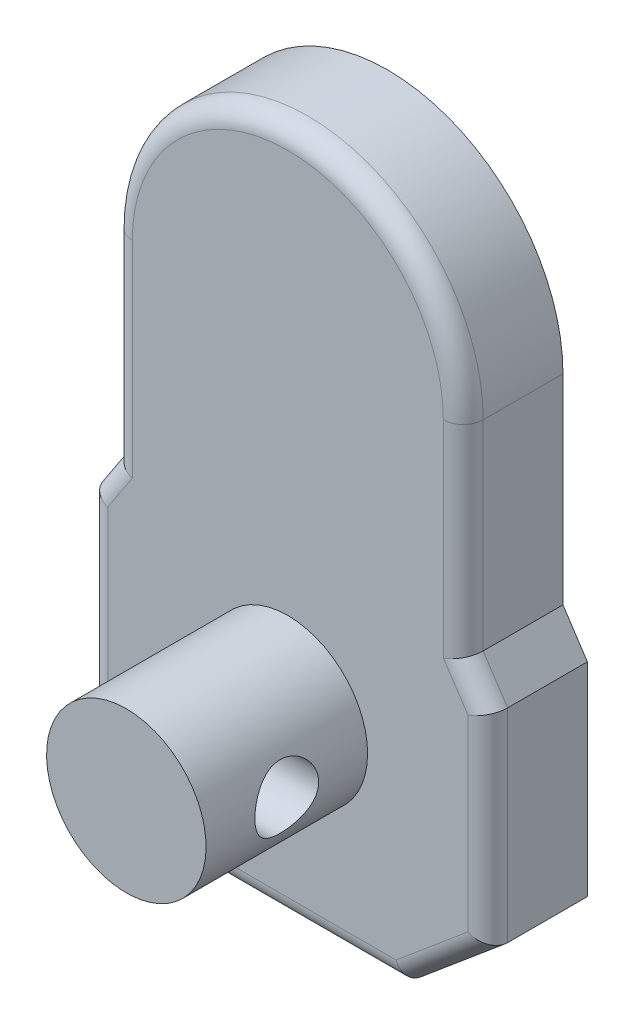
SolidWorks part; units mm, degrees
material "PW100:Mi:0:1:Ar:0:-1:C1:1:2:3:Re:27:"
ref_plane "Front" through (0, 0, 0) normal (0, 0, 1) x (1, 0, 0)
ref_plane "Top" through (0, 0, 0) normal (0, 1, 0) x (1, 0, 0)
ref_plane "Right" through (0, 0, 0) normal (1, 0, 0) x (0, 0, -1)
sketch "Support-Front-Cylinder" plane through (0, 0, 0) normal (0, 0, 1) x (1, 0, 0)
  line L0 (0, -23) -> (0, 50.4) construction
  line L1 (20.05, 0) -> (-20.05, 0) construction
  line L23 (-9.0631, 28.5738) -> (9.0631, 37.0262) construction
  line L28 (5.4164, -18.5) -> (5.4164, -20)
  line L32 (16, -9) -> (-16, 9) construction
  line L33 (-16, -9) -> (16, 9) construction
  line L34 (5.4164, -20) -> (-5.4164, -20)
  line L35 (-5.4164, -18.5) -> (-5.4164, -20)
  line L45 (0, -18.5) -> (-5.4164, -17.0487) construction
  line L46 (-20.05, 9) -> (-17.6, 12.7206)
  line L47 (20.05, 0) -> (20.05, -11.4)
  line L48 (-5.373, 24.3661) -> (0, 32.8) construction
  line L49 (-20.05, 0) -> (-20.05, -11.4)
  line L50 (-9.0631, 28.5738) -> (-5.373, 24.3661) construction
  line L51 (20.05, -11.4) -> (11.5885, -18.5)
  line L52 (-13.75, 0) -> (-7.0166, -18.5)
  line L53 (-7.0166, -18.5) -> (7.0166, -18.5)
  line L54 (0, -18.5) -> (0, -23) construction
  line L55 (13.75, 0) -> (7.0166, -18.5)
  line L56 (-20.05, -11.4) -> (-11.5885, -18.5)
  line L57 (11.5885, -18.5) -> (7.0166, -18.5)
  line L58 (-11.5885, -18.5) -> (-7.0166, -18.5)
  line L59 (20.05, -11.4) -> (-20.05, -11.4) construction
  line L60 (20.05, 0) -> (20.05, 9)
  line L61 (-20.05, 0) -> (-20.05, 9)
  line L62 (17.6, 12.7206) -> (17.6, 32.8)
  line L63 (-17.6, 12.7206) -> (-17.6, 32.8)
  line L64 (2.5, -20) -> (2.5, -23)
  line L65 (-2.5, -20) -> (-2.5, -23)
  line L66 (2.5, -23) -> (-2.5, -23)
  line L67 (-11.7451, 0.3392) -> (-5.4164, -17.0487)
  line L68 (11.7451, 0.3392) -> (5.4164, -17.0487)
  line L69 (5.4164, -17.0487) -> (-5.4164, -17.0487)
  line L70 (5.4164, -18.5) -> (5.4164, -17.0487) construction
  line L71 (-5.4164, -18.5) -> (-5.4164, -17.0487) construction
  line L72 (17.6, 32.8) -> (-17.6, 32.8) construction
  line L73 (20.05, 9) -> (17.6, 12.7206)
  line L75 (-5.373, 24.3661) -> (0, 22.8) construction
  circle A18 centre (0, 0) radius 9.65
  circle A29 centre (16, 9) radius 2.4
  arc A30 (13.75, 0) -> (-13.75, 0) centre (0, 0) ccw
  circle A31 centre (-16, 9) radius 2.4
  circle A32 centre (-16, -9) radius 2.4
  circle A33 centre (16, -9) radius 2.4
  arc A34 (20.05, 9) -> (17.6, 12.7206) centre (16, 9) ccw
  arc A35 (-20.05, 9) -> (-17.6, 12.7206) centre (-16, 9) cw
  arc A36 (17.6, 32.8) -> (0, 50.4) centre (0, 32.8) ccw
  arc A37 (-17.6, 32.8) -> (0, 50.4) centre (0, 32.8) cw
  arc A38 (17.6, 32.8) -> (-17.6, 32.8) centre (0, 32.8) cw
  arc A39 (11.7451, 0.3392) -> (-11.7451, 0.3392) centre (0, 0) ccw
  arc A40 (13.75, 0) -> (-13.75, 0) centre (0, 0) cw construction
  circle A41 centre (0, 32.8) radius 10
  circle A42 centre (-5.373, 24.3661) radius 2.5
  circle A43 centre (-9.0631, 28.5738) radius 3.75
  circle A44 centre (9.0631, 37.0262) radius 2.5
  circle A45 centre (-5.373, 24.3661) radius 0.75
  circle A46 centre (9.0631, 37.0262) radius 0.75
  point P3 (0, 0)
  point P6 (0, 0)
  point P16 (0, -20)
  dimension "D4" = 4.8
  dimension "D5" = 1.5
  dimension "D14" = 3
  dimension "D15" = 73.4
  dimension "D20" = 1.5
  dimension "D21" = 25
  dimension "D10" = 19.3
  dimension "D24" = 27.5
  dimension "D12" = 35.2
  dimension "D17" = 20
  dimension "D18" = 5
  dimension "D19" = 7.5
  dimension "D3" = 40.1
  dimension "D6" = 18.5
  dimension "D7" = 32
  dimension "D8" = 18
  dimension "D9" = 100
  dimension "D16" = 2
  dimension "D22" = 15
  dimension "D23" = 32.8
  dimension "D26" = 40
  dimension "Thickn-Elect" = 5
sketch "Support-Right" plane through (0, 0, 0) normal (1, 0, 0) x (0, 0, -1)
  line L0 (96.6074, 0) -> (-156.5, 0) construction
  line L1 (-140.3, -18.5) -> (-140.3, 50.4)
  line L2 (0, -18.5) -> (0, 13.75)
  line L3 (0, 13.75) -> (-90.3, 13.75)
  line L4 (87.4074, 9.65) -> (96.6074, 9.65)
  line L5 (-140.3, 50.4) -> (-95.3, 50.4)
  line L6 (-90.3, 15.2) -> (-85.3, 15.2)
  line L7 (-95.3, 50.4) -> (-95.3, -18.5)
  line L8 (-85.3, 15.2) -> (-85.3, 50.4) construction
  line L9 (-11.7, 17.7) -> (-11.7, 47.9)
  line L10 (-14.2, 50.4) -> (-90.3, 50.4)
  line L11 (-85.3, 50.4) -> (-84.9, 50.8)
  line L12 (-95.3, -18.5) -> (-140.3, -18.5)
  line L13 (-95.3, 50.4) -> (-90.3, 50.4)
  line L14 (-90.3, 50.4) -> (-90.3, 15.2)
  line L15 (0, 9.65) -> (-31, 9.65) construction
  line L16 (-90.3, 15.2) -> (-90.3, -18.5)
  line L17 (-90.3, -18.5) -> (-95.3, -18.5)
  line L18 (-85.3, 15.2) -> (-85.3, -18.5) construction
  line L19 (-90.3, -18.5) -> (0, -18.5)
  line L20 (-140.3, -20.75) -> (-140.3, -18.5) construction
  line L21 (-140.3, 32.8) -> (-9.2, 32.8) construction
  line L22 (-9.2, 50.4) -> (-9.2, 15.2) construction
  line L23 (-9.2, 15.2) -> (-11.7, 15.2) construction
  line L24 (-9.2, 50.4) -> (-11.7, 50.4) construction
  line L25 (-156.5, 8) -> (-156.5, -8)
  line L26 (-156.5, -8) -> (-140.3, -8)
  line L27 (-84.9, 50.8) -> (-90.7, 50.8)
  line L28 (-90.7, 50.8) -> (-90.3, 50.4)
  line L29 (-156.5, 8) -> (-140.3, 8)
  line L30 (-14, 13.75) -> (-14, -18.5) construction
  line L31 (-90.7, 14.8) -> (-90.3, 15.2)
  line L32 (96.6074, 9.65) -> (96.6074, -9.65)
  line L35 (87.4074, 9.65) -> (-106.9074, 9.65)
  line L36 (-106.9074, 9.65) -> (-106.9074, -9.65)
  line L37 (87.4074, -9.65) -> (-106.9074, -9.65)
  line L38 (-84.9, 14.8) -> (-90.7, 14.8)
  line L40 (87.4074, -9.65) -> (96.6074, -9.65)
  line L41 (-17.5, 50.4) -> (0, 50.4) construction
  line L42 (-9.2, 32.8) -> (0, 32.8) construction
  line L43 (-85.3, 15.2) -> (-84.9, 14.8)
  line L44 (-121.6287, -20.75) -> (-120.4574, -18.5)
  line L45 (-130.7862, -20.75) -> (-131.9574, -18.5)
  line L46 (-121.6287, -20.75) -> (-130.7862, -20.75)
  line L47 (-106.9074, -9.65) -> (-126.2074, -9.65) construction
  line L48 (83.6574, 9.65) -> (82.4074, 8.4)
  line L49 (-126.2074, -9.65) -> (-126.2074, 9.65) construction
  line L50 (-31, 13.75) -> (-31, -18.5) construction
  line L51 (82.4074, 8.4) -> (81.1574, 9.65)
  line L52 (82.4074, 9.65) -> (82.4074, -9.65) construction
  line L53 (-85.3, 15.2) -> (0, 15.2)
  line L54 (-90.3, 50.4) -> (-17.5, 50.4) construction
  line L55 (82.4074, -8.4) -> (81.1574, -9.65)
  line L56 (83.6574, -9.65) -> (82.4074, -8.4)
  line L57 (-126.2074, 9.65) -> (-106.9074, 9.65) construction
  line L58 (0, 15.2) -> (0, 13.75) construction
  line L60 (0, -23) -> (0, -18.5) construction
  line L63 (-122.7862, -20.75) -> (-123.9574, -23)
  line L64 (0, -9.65) -> (-31, -9.65) construction
  line L69 (-123.9574, -23) -> (-128.4574, -23)
  line L70 (-126.2074, -23) -> (-126.2074, -18.5) construction
  line L71 (-140.3, -20.75) -> (0, -20.75) construction
  line L72 (-129.6287, -20.75) -> (-128.4574, -23)
  line L73 (-140.3, -20.75) -> (-140.3, -23) construction
  line L74 (-140.3, -23) -> (0, -23) construction
  line L75 (-130.3, 50.4) -> (-130.3, -18.5)
  arc A0 (-14.2, 50.4) -> (-11.7, 47.9) centre (-14.2, 47.9) cw
  arc A1 (-14.2, 15.2) -> (-11.7, 17.7) centre (-14.2, 17.7) ccw
  circle A2 centre (-148.4, 0) radius 3.2
  circle A3 centre (87.4074, 0) radius 3.2
  point P13 (-140.3, 32.8)
  point P18 (11.5, 0)
  point P44 (87.4074, 0)
  point P50 (-106.9074, 0)
  point P54 (96.6074, 0)
  point P61 (-11.7, 32.8)
  point P63 (-14, 0)
  point P71 (-196.35, 0)
ref_plane "Plane1" through (0, 0, 130.3) normal (0, 0, 1) x (1, 0, 0)
sketch "Sketch1" plane through (0, 0, 130.3) normal (0, 0, 1) x (1, 0, 0)
  line L0 (20.05, 9) -> (17.6, 12.7206) construction
  line L1 (-20.05, 9) -> (-17.6, 12.7206) construction
  line L2 (20.05, 9) -> (17.6, 12.7206)
  line L3 (-20.05, 0) -> (-20.05, 9) construction
  line L4 (-20.05, 0) -> (-20.05, -11.4) construction
  line L5 (-20.05, -11.4) -> (-11.5885, -18.5) construction
  line L6 (-11.5885, -18.5) -> (-7.0166, -18.5) construction
  line L7 (-17.6, 12.7206) -> (-17.6, 32.8) construction
  line L8 (-7.0166, -18.5) -> (7.0166, -18.5) construction
  line L9 (20.05, 0) -> (20.05, 9) construction
  line L10 (20.05, 0) -> (20.05, -11.4) construction
  line L11 (20.05, -11.4) -> (11.5885, -18.5) construction
  line L12 (11.5885, -18.5) -> (7.0166, -18.5) construction
  line L13 (17.6, 12.7206) -> (17.6, 32.8) construction
  line L14 (-20.05, 9) -> (-17.6, 12.7206)
  line L16 (-20.05, -11.4) -> (-11.5885, -18.5)
  line L18 (-17.6, 12.7206) -> (-17.6, 32.8)
  line L19 (-20.05, 0) -> (-20.05, 9)
  line L20 (-20.05, 0) -> (-20.05, -11.4)
  line L22 (-11.5885, -18.5) -> (-7.0166, -18.5)
  line L23 (-7.0166, -18.5) -> (7.0166, -18.5)
  line L24 (20.05, 0) -> (20.05, 9)
  line L25 (20.05, 0) -> (20.05, -11.4)
  line L26 (20.05, -11.4) -> (11.5885, -18.5)
  line L27 (11.5885, -18.5) -> (7.0166, -18.5)
  line L28 (17.6, 12.7206) -> (17.6, 32.8)
  arc A6 (0, 50.4) -> (-17.6, 32.8) centre (0, 32.8) ccw construction
  arc A7 (17.6, 32.8) -> (0, 50.4) centre (0, 32.8) ccw construction
  arc A14 (0, 50.4) -> (-17.6, 32.8) centre (0, 32.8) ccw
  arc A15 (17.6, 32.8) -> (0, 50.4) centre (0, 32.8) ccw
extrude "Body" add sketch "Sketch1" along normal blind 10
ref_plane "Plane2" through (0, 0, 14) normal (0, 0, 1) x (1, 0, 0)
ref_plane "Plane3" through (0, 0, 148.4) normal (0, 0, 1) x (1, 0, 0)
sketch "Sketch3" plane through (0, 0, 0) normal (1, 0, 0) x (0, 0, -1)
  line L7 (-140.3, -18.5) -> (-140.3, 50.4) construction
  line L8 (-156.5, 8) -> (-156.5, -8) construction
  line L9 (-156.5, 8) -> (-140.3, 8) construction
  line L10 (96.6074, 0) -> (-156.5, 0) construction
  line L11 (-140.3, 0) -> (-140.3, 8)
  line L12 (-156.5, 8) -> (-156.5, 0)
  line L13 (-156.5, 8) -> (-140.3, 8)
  line L15 (-140.3, 0) -> (-156.5, 0)
  line L16 (96.6074, 0) -> (-156.5, 0) construction
revolve "Motor-Body" add sketch "Sketch3" angle 360 about L16
sketch "Sketch7" plane through (0, 0, 0) normal (1, 0, 0) x (0, 0, -1)
  circle A0 centre (-148.4, 0) radius 3.2 construction
  circle A1 centre (-148.4, 0) radius 3.2
extrude "Rear-Mounting" cut sketch "Sketch7" against normal through all and the other way through all
sketch "Sketch8" plane through (0, 0, 130.3) normal (0, 0, 1) x (1, 0, 0)
  circle A0 centre (16, -9) radius 2.4 construction
  circle A1 centre (-16, -9) radius 2.4 construction
  circle A2 centre (-16, 9) radius 2.4 construction
  circle A3 centre (16, 9) radius 2.4 construction
  circle A4 centre (16, -9) radius 2.4
  circle A5 centre (-16, -9) radius 2.4
  circle A6 centre (-16, 9) radius 2.4
  circle A7 centre (16, 9) radius 2.4
extrude "Hole" cut sketch "Sketch8" along normal blind 8.5
fillet "Fillet4" radius 2 10 edges at (-17.6, 22.7603, 140.3) (-18.825, 10.8603, 140.3) (-20.05, -1.2, 140.3) (-15.8193, -14.95, 140.3) (0, -18.5, 140.3) (15.8193, -14.95, 140.3) (20.05, -1.2, 140.3) (0, 50.4, 140.3) (18.825, 10.8603, 140.3) (17.6, 22.7603, 140.3)
equation "\"Length-Total@Support-Right\" = \"Stroke@Support-Right\"+113.7"
